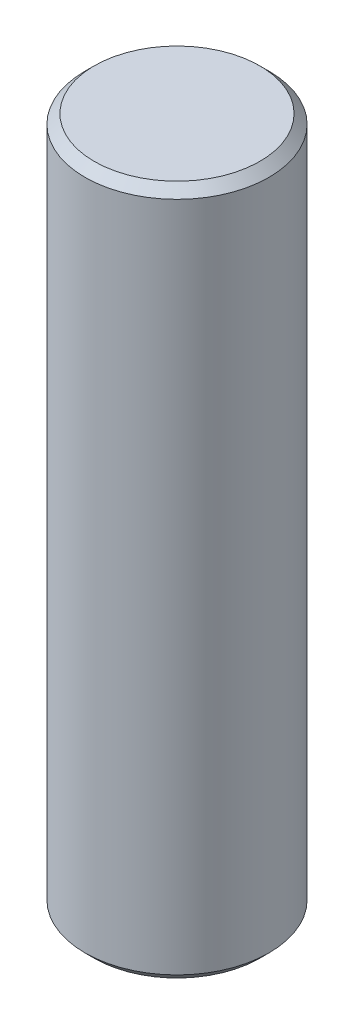
SolidWorks part; units mm, degrees
material "铸造合金钢"
ref_plane "前视基准面" through (0, 0, 0) normal (0, 0, 1) x (1, 0, 0)
ref_plane "上视基准面" through (0, 0, 0) normal (0, 1, 0) x (1, 0, 0)
ref_plane "右视基准面" through (0, 0, 0) normal (1, 0, 0) x (0, 0, -1)
sketch "草图1" plane through (0, 0, 0) normal (0, 1, 0) x (1, 0, 0)
  circle A0 centre (0, 0) radius 2
  dimension "D1" = 4
extrude "凸台-拉伸1" add sketch "草图1" along normal blind 15
chamfer "倒角1" distance 0.2 angle 45 2 edges at (0, 0, 2) (0, 15, 2)
